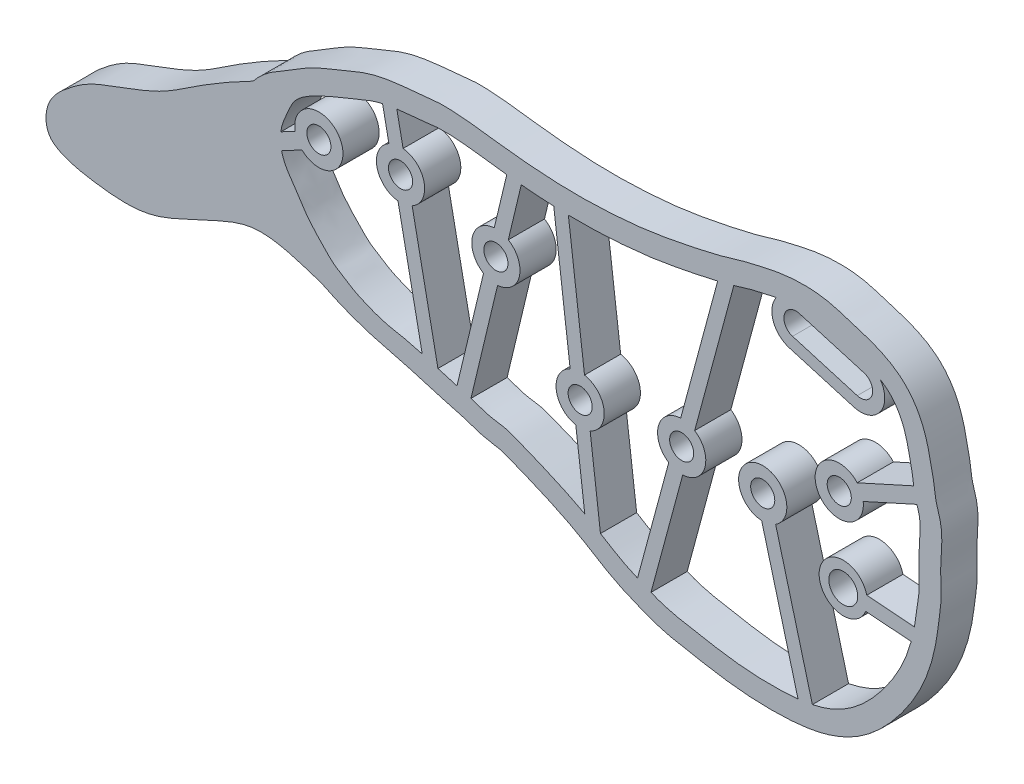
SolidWorks part; units mm, degrees
ref_plane "Спереди" through (0, 0, 0) normal (0, 0, 1) x (1, 0, 0)
ref_plane "Сверху" through (0, 0, 0) normal (0, 1, 0) x (1, 0, 0)
ref_plane "Справа" through (0, 0, 0) normal (1, 0, 0) x (0, 0, -1)
other "Configuration Table"
sketch "Sketch1" plane through (0, 0, 0) normal (0, 0, 1) x (1, 0, 0)
  line L0 (-49.8798, -35.1852) -> (-46.5286, -51.8261) construction
  line L5 (-47.1793, -51.6343) -> (-49.1909, -41.6452)
  line L6 (-49.9442, -37.9045) -> (-50.4687, -35.3004)
  line L8 (-48.7678, -37.6676) -> (-49.2862, -35.0938)
  line L9 (-48.0145, -41.4083) -> (-45.8772, -52.0216)
  line L10 (-43.7178, -52.6384) -> (-39.5688, -35.3106) construction
  line L11 (-6.4818, -51.4155) -> (-12.265, -50.9822) construction
  line L12 (-41.2097, -39.5871) -> (-40.1701, -35.2453)
  line L14 (-38.9662, -35.3706) -> (-40.0427, -39.8665)
  line L15 (-42.0983, -43.298) -> (-44.2973, -52.4822)
  line L16 (-40.9312, -43.5774) -> (-43.1396, -52.8005)
  line L17 (-33.0514, -56.7428) -> (-35.6666, -35.5833) construction
  line L18 (-36.274, -35.5605) -> (-34.9138, -46.5662)
  line L19 (-35.0602, -35.5983) -> (-33.7228, -46.419)
  line L20 (-28.7671, -59.0348) -> (-22.0114, -33.9745) construction
  line L21 (-22.6779, -34.1417) -> (-25.7465, -45.5248)
  line L22 (-21.3407, -33.7919) -> (-24.5879, -45.8372)
  line L23 (-15.4183, -60.7418) -> (-18.9436, -47.5231) construction
  line L24 (-16.018, -60.8216) -> (-19.0317, -49.5212)
  line L25 (-14.8259, -60.6345) -> (-17.8722, -49.2119)
  line L26 (-6.3189, -41.3366) -> (-12.597, -44.1796) construction
  line L27 (-6.4229, -40.7251) -> (-11.1066, -42.846)
  line L28 (-6.1531, -41.9202) -> (-10.6115, -43.9391)
  line L29 (-16.1872, -34.0479) -> (-10.8235, -35.627) construction
  line L34 (-34.1152, -53.0271) -> (-34.4457, -50.3531) construction
  line L35 (-34.4457, -50.3531) -> (-33.7016, -56.3739)
  line L37 (-33.2548, -50.2059) -> (-32.3983, -57.1358)
  line L43 (-26.7397, -49.209) -> (-29.3266, -58.8049)
  line L45 (-25.5811, -49.5214) -> (-28.2081, -59.266)
  line L52 (-15.9048, -33.0886) -> (-10.541, -34.6677)
  line L55 (-42.0983, -43.298) -> (-44.2973, -52.4822) construction
  line L56 (-6.36, -50.823) -> (-10.3177, -50.5264)
  line L57 (-6.36, -50.823) -> (-10.3177, -50.5264)
  line L58 (-16.4697, -35.0072) -> (-11.1059, -36.5863)
  line L59 (-16.1872, -34.0479) -> (-10.8235, -35.627) construction
  line L60 (-15.6224, -32.1293) -> (-10.2586, -33.7084)
  line L61 (-16.7521, -35.9665) -> (-11.3883, -37.5456)
  line L62 (-6.6306, -52.0061) -> (-10.4073, -51.7231)
  line L63 (-58.9395, -42.2399) -> (-55.753, -40.5323) construction
  line L64 (-57.718, -40.9046) -> (-58.9116, -41.5442)
  line L65 (-57.1512, -41.9623) -> (-58.8458, -42.8704)
  arc A2 (-48.0145, -41.4083) -> (-48.7678, -37.6676) centre (-48.9794, -39.6564) ccw
  circle A3 centre (-48.9794, -39.6564) radius 1
  arc A4 (-40.9312, -43.5774) -> (-40.0427, -39.8665) centre (-41.0705, -41.5823) ccw
  circle A5 centre (-41.0705, -41.5823) radius 1
  arc A6 (-33.2548, -50.2059) -> (-33.7228, -46.419) centre (-34.0843, -48.386) ccw
  circle A7 centre (-34.0843, -48.386) radius 1
  arc A8 (-25.5811, -49.5214) -> (-24.5879, -45.8372) centre (-25.6638, -47.5231) ccw
  circle A9 centre (-25.6638, -47.5231) radius 1
  circle A11 centre (-18.9436, -47.5231) radius 1
  arc A14 (-11.1066, -42.846) -> (-10.6115, -43.9391) centre (-12.597, -44.1796) ccw
  circle A15 centre (-12.597, -44.1796) radius 1
  arc A20 (-17.8722, -49.2119) -> (-19.0317, -49.5212) centre (-18.9436, -47.5231) ccw
  arc A26 (-10.3177, -50.5264) -> (-10.4073, -51.7231) centre (-12.265, -50.9822) ccw
  circle A29 centre (-12.265, -50.9822) radius 1.2
  arc A30 (-15.9048, -33.0886) -> (-16.4697, -35.0072) centre (-16.1872, -34.0479) ccw
  arc A31 (-11.1059, -36.5863) -> (-10.541, -34.6677) centre (-10.8235, -35.627) ccw
  arc A32 (-49.9442, -37.9045) -> (-49.1909, -41.6452) centre (-48.9794, -39.6564) ccw
  arc A33 (-15.6224, -32.1293) -> (-16.7521, -35.9665) centre (-16.1872, -34.0479) ccw
  arc A34 (-11.3883, -37.5456) -> (-10.2586, -33.7084) centre (-10.8235, -35.627) ccw
  arc A37 (-41.2097, -39.5871) -> (-42.0983, -43.298) centre (-41.0705, -41.5823) ccw
  arc A42 (-34.9138, -46.5662) -> (-34.4457, -50.3531) centre (-34.0843, -48.386) ccw
  arc A47 (-25.7465, -45.5248) -> (-26.7397, -49.209) centre (-25.6638, -47.5231) ccw
  arc A49 (-54.8354, -41.618) -> (-54.8321, -41.6152) centre (-55.753, -40.5323) ccw
  arc A50 (-57.1512, -41.9623) -> (-57.718, -40.9046) centre (-55.753, -40.5323) ccw
  circle A51 centre (-55.753, -40.5323) radius 1
  spline S1 degree 3 poles (-58.7581, -48.9728) (-59.7104, -48.3693) (-60.601, -47.7494) (-61.439, -47.078) (-62.1184, -46.3069) (-62.5768, -45.5749) (-62.8752, -44.6554) (-62.9472, -43.8318) (-62.9111, -43.0968) (-62.7679, -42.1814) (-62.4279, -41.1031) (-61.9297, -40.1186) (-61.4448, -39.3508) (-60.8782, -38.6247) (-60.0099, -37.8334) (-59.0035, -37.2266) (-58.1744, -36.7533) (-57.3271, -36.2193) (-56.3554, -35.6419) (-55.2169, -35.133) (-54.2864, -34.7926) (-53.4311, -34.4203) (-52.4291, -33.9883) (-51.2557, -33.5906) (-50.0717, -33.365) (-49.0452, -33.2111) (-47.8281, -33.1277) (-47.1214, -33.049) (-45.8394, -32.8805) (-44.6534, -32.9112) (-43.5686, -32.9952) (-42.1571, -33.1582) (-40.5095, -33.3844) (-38.5454, -33.593) (-35.9409, -33.7854) (-33.3406, -33.8134) (-30.7567, -33.6586) (-28.7942, -33.4693) (-26.9201, -33.1767) (-24.9503, -32.7873) (-23.3497, -32.4416) (-22.2655, -32.1636) (-21.6495, -31.9895) (-21.2094, -31.858) (-20.7095, -31.6941) (-19.878, -31.4801) (-19.1412, -31.3211) (-18.0288, -31.0648) (-16.5225, -30.8399) (-14.9286, -30.7968) (-13.4817, -31.0194) (-12.6301, -31.2555) (-12.133, -31.42) (-11.6411, -31.5679) (-10.8921, -31.7911) (-9.8671, -32.12) (-8.5679, -32.6816) (-7.2519, -33.5682) (-6.2079, -34.8481) (-5.5594, -36.1965) (-5.2408, -37.2885) (-5.0596, -38.0988) (-4.9425, -38.6834) (-4.8586, -39.115) (-4.7764, -39.4986) (-4.6916, -40.0045) (-4.6394, -40.4888) (-4.5811, -40.8774) (-4.4823, -41.2228) (-4.2813, -41.832) (-4.1203, -42.5843) (-4.0747, -43.3775) (-4.1171, -44.2931) (-4.1787, -45.2641) (-4.1993, -45.9027) (-4.1608, -46.9025) (-4.1506, -47.8696) (-4.2242, -48.6554) (-4.293, -49.0787) (-4.341, -49.3743) (-4.4, -49.8432) (-4.483, -50.5058) (-4.5958, -51.1879) (-4.7781, -52.0596) (-5.1851, -53.5287) (-6.0146, -55.4591) (-7.3401, -57.5243) (-8.9971, -59.4846) (-11.088, -61.2131) (-13.7073, -62.3173) (-16.2947, -62.6859) (-18.6823, -62.7476) (-21.1287, -62.5988) (-23.0787, -62.2999) (-24.5778, -62.0304) (-25.6889, -61.8329) (-26.8868, -61.5905) (-27.9556, -61.2829) (-28.7638, -60.9667) (-29.2891, -60.7458) (-29.7912, -60.5419) (-30.3561, -60.3078) (-30.9518, -60.0302) (-31.6951, -59.6404) (-32.5624, -59.1303) (-33.5293, -58.5308) (-34.7253, -57.8223) (-36.2969, -57.0567) (-38.0088, -56.2932) (-39.3047, -55.7945) (-40.3059, -55.3706) (-40.6535, -55.2581) (-41.0437, -55.1903) (-41.6818, -55.1072) (-42.474, -54.9095) (-43.0705, -54.6973) (-43.5262, -54.5405) (-43.9971, -54.4055) (-44.7148, -54.2168) (-45.6675, -53.9511) (-47.1182, -53.5215) (-48.8494, -53.0092) (-51.0345, -52.5074) (-53.2229, -51.7923) (-54.8479, -51.0605) (-56.3053, -50.3491) (-57.5646, -49.6747) (-58.7581, -48.9728) (-59.7104, -48.3693) (-60.601, -47.7494) knots -0.027589 -0.015625 -0.007812 0 0.007812 0.015625 0.019531 0.023437 0.027344 0.03125 0.035156 0.039062 0.046875 0.054687 0.059556 0.063462 0.070312 0.078125 0.085937 0.09375 0.101562 0.109375 0.117187 0.125 0.132812 0.140625 0.148437 0.15625 0.164062 0.171875 0.179687 0.1875 0.195312 0.203125 0.21875 0.234375 0.25 0.28125 0.296875 0.3125 0.328125 0.34375 0.359375 0.367187 0.371094 0.375 0.378906 0.382812 0.390625 0.398437 0.40625 0.421875 0.429687 0.433594 0.4375 0.441406 0.445312 0.453125 0.460937 0.46875 0.476562 0.484375 0.492187 0.496094 0.5 0.503906 0.505859 0.507812 0.511719 0.515625 0.519531 0.523437 0.527344 0.53125 0.535156 0.539062 0.546875 0.554687 0.5625 0.566406 0.568359 0.570312 0.574219 0.578125 0.582031 0.585937 0.59375 0.609375 0.625 0.640625 0.65625 0.671875 0.6875 0.703125 0.71875 0.734375 0.742187 0.75 0.757812 0.765625 0.769531 0.773437 0.777344 0.78125 0.785156 0.789062 0.796875 0.804687 0.8125 0.828125 0.84375 0.851562 0.859375 0.863281 0.867187 0.871094 0.875 0.878906 0.882812 0.886719 0.890625 0.898437 0.90625 0.921875 0.9375 0.953125 0.964598 0.972411 0.984375 0.992187 1 1.007812 1.015625 1.019531 only from (-59.7001, -48.3666) to (-59.7001, -48.3666)
  spline S2 degree 3 poles (-54.5333, -48.7736) (-54.3278, -49.1341) (-56.9345, -46.3498) (-57.1292, -45.7523) (-58.9885, -43.3177) (-59.0573, -41.4) (-58.1736, -39.4863) (-57.7325, -38.3952) (-55.4019, -37.1517) (-53.2414, -36.357) (-51.2775, -35.3982) (-49.5355, -35.1222) (-48.3071, -34.966) (-47.2996, -34.9312) (-45.9793, -34.697) (-43.9654, -34.742) (-40.8542, -35.194) (-36.962, -35.5881) (-33.9262, -35.6271) (-31.9892, -35.554) (-30.8887, -35.4887) (-29.5808, -35.3714) (-27.6433, -35.1578) (-24.6742, -34.6016) (-21.912, -33.9992) (-19.9812, -33.3713) (-19.0765, -33.1767) (-17.7192, -32.8438) (-15.8054, -32.5785) (-14.0131, -32.7113) (-11.5739, -33.5264) (-8.8287, -34.1518) (-7.065, -36.9423) (-6.7879, -38.7114) (-6.4527, -40.2945) (-6.4104, -41.2062) (-5.9587, -42.4484) (-5.8567, -43.2131) (-5.9542, -44.844) (-6.0378, -46.2993) (-5.8798, -47.7388) (-6.1409, -49.2063) (-6.4685, -52.3712) (-8.2087, -56.1917) (-12.2182, -60.2134) (-15.6942, -60.8453) (-17.4574, -60.9255) (-18.4504, -60.9397) (-19.983, -60.9127) (-22.1617, -60.661) (-24.8025, -60.1784) (-26.9948, -59.7888) (-28.675, -59.0656) (-30.7159, -58.261) (-33.245, -56.49) (-36.0164, -55.2272) (-37.9357, -54.4025) (-39.0581, -53.9788) (-40.2192, -53.4582) (-41.5646, -53.3766) (-42.8693, -52.851) (-45.1061, -52.2938) (-48.6636, -51.1067) (-49.9566, -51.138) (-52.6241, -50.0674) (-54.5333, -48.7736) (-54.3278, -49.1341) (-56.9345, -46.3498) knots -0.053539 -0.040554 -0.0352 0 0.008418 0.024992 0.034759 0.054839 0.065896 0.084166 0.104395 0.11788 0.139207 0.153886 0.158466 0.167836 0.177148 0.189373 0.214163 0.249835 0.279723 0.284249 0.294647 0.305206 0.314606 0.339694 0.375025 0.37997 0.386562 0.396484 0.411656 0.431742 0.437535 0.469592 0.482501 0.504001 0.506417 0.516135 0.523104 0.532522 0.536639 0.545133 0.566484 0.569737 0.578233 0.624864 0.662471 0.68872 0.696194 0.699273 0.709375 0.72807 0.744781 0.765339 0.774026 0.78277 0.810922 0.837688 0.846033 0.85436 0.862697 0.872259 0.882004 0.891572 0.921379 0.946461 0.959446 0.9648 1 1.008418 1.024992 1.034759 only from (-55.5648, -47.8082) to (-55.5648, -47.8082)
  spline S3 degree 3 poles (-61.2035, -39.0465) (-62.6266, -39.7878) (-65.2104, -41.2073) (-68.8391, -43.8371) (-72.316, -44.9961) (-74.9893, -46.057) (-76.7811, -47.3826) (-78.4745, -48.9002) (-78.4678, -51.4704) (-76.4876, -52.5204) (-73.8899, -52.9864) (-69.8015, -53.368) (-66.6062, -51.6264) (-63.7164, -50.3566) (-60.4803, -48.9267) (-57.3234, -50.1544) (-55.5571, -50.7128) knots 0 0 0 0 0.104944 0.193163 0.290921 0.343523 0.379953 0.436893 0.487498 0.515193 0.574608 0.662727 0.775391 0.804004 0.87067 1 1 1 1
  point P15 (-13.5054, -34.8374)
  point P22 (-13.5054, -34.8374)
  point P47 (-40.2435, -39.3137)
  point P49 (0, 0)
  point P51 (-52.7746, -39.2302)
  point P55 (-50.0252, -35.3334)
  point P61 (-46.7989, -51.5964)
  point P71 (-57.779, -41.5162)
  point P75 (-41.5787, -39.3137)
  point P87 (-42.0944, -40.4576)
  point P91 (-57.4384, -38.4738)
  point P106 (-59.4037, -39.8354)
  point P113 (-58.3401, -39.8354)
  point P118 (-57.7671, -40.4626)
  point P120 (-58.7055, -41.9202)
  point P122 (-57.9234, -43.7164)
  point P123 (-56.7212, -45.5248)
  point P124 (-57.1874, -43.5759)
  point P125 (-56.7862, -46.5662)
  point P126 (-55.5648, -47.8647)
  point P127 (-56.4744, -46.8095)
  point P128 (-57.2803, -45.2677)
  point P129 (-58.0313, -43.7073)
  point P131 (-57.5266, -45.2677)
  point P132 (-58.8339, -41.0825)
  point P134 (-58.4528, -43.8764)
  point P136 (-53.0343, -49.7791)
  point P138 (-50.8875, -50.7285)
  point P139 (-55.5648, -47.8082)
  point P140 (0, 0)
  point P141 (0, 0)
  point P142 (0, 0)
  point P143 (-49.1022, -41.8161)
  point P145 (0, 0)
  point P147 (-49.1022, -39.0465)
  point P149 (-55.753, -40.5323)
  point P151 (0, 0)
  point P153 (0, 0)
  point P154 (0, 0)
  dimension "D19" = 2
  dimension "D22" = 4
  dimension "D6" = 0.6
  dimension "D10" = 0.6
  dimension "D14" = 0.6
  dimension "D15" = 0.6
  dimension "D11" = 0.6
  dimension "D12" = 0.6
  dimension "D4" = 0.6
  dimension "D5" = 0.6
  dimension "D8" = 0.6
  dimension "D3" = 0.6
  dimension "D9" = 0.6
  dimension "D16" = 0.6
  dimension "D13" = 1
  dimension "D17" = 0.6
  dimension "D18" = 0.6
  dimension "D2" = 0.6
  dimension "D7" = 0.6
  dimension "D21" = 6.83
  dimension "D23" = 14.72
  dimension "D20" = 8.14
extrude "Boss-Extrude2" add sketch "Sketch1" along normal blind 3
equation "\"R small\"= 2"
equation "\"R big\"= 4"
equation "\"width\"= 0.6"
equation "\"D5@Sketch1\"=\"width\""
equation "\"D4@Sketch1\"=\"width\""
equation "\"D3@Sketch1\"=\"width\""
equation "\"D9@Sketch1\"=\"width\""
equation "\"D8@Sketch1\"=\"width\""
equation "\"D6@Sketch1\"=\"width\""
equation "\"D10@Sketch1\"=\"width\""
equation "\"D16@Sketch1\"=\"width\""
equation "\"D11@Sketch1\"=\"width\""
equation "\"D12@Sketch1\"=\"width\""
equation "\"D14@Sketch1\"=\"width\""
equation "\"D15@Sketch1\"=\"width\""
equation "\"border width\"= 1"
equation "\"D13@Sketch1\"=\"border width\""
equation "\"D17@Sketch1\"=\"width\""
equation "\"D18@Sketch1\"=\"width\""
equation "\"depth\"= 3"
equation "\"D2@Sketch1\"=\"width\""
equation "\"D7@Sketch1\"=\"width\""
equation "\"D19@Sketch1\"=\"R small\""
equation "\"D22@Sketch1\"=\"R big\""
